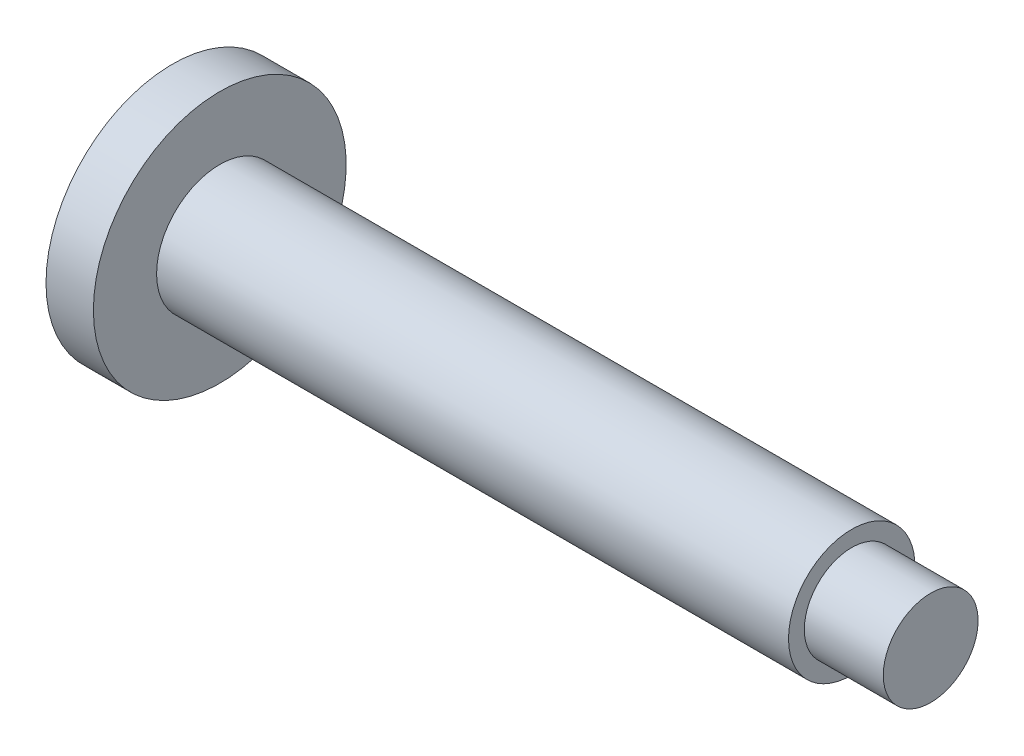
SolidWorks part; units mm, degrees
ref_plane "Front Plane" through (0, 0, 0) normal (0, 0, 1) x (1, 0, 0)
ref_plane "Top Plane" through (0, 0, 0) normal (0, 1, 0) x (1, 0, 0)
ref_plane "Right Plane" through (0, 0, 0) normal (1, 0, 0) x (0, 0, -1)
sketch "Sketch1" plane through (0, 0, 0) normal (0, 0, 1) x (1, 0, 0)
  line L0 (0, 0) -> (52.5167, 0) construction
  line L1 (0, 0) -> (0, 8)
  line L2 (0, 8) -> (3, 8)
  line L3 (3, 8) -> (3, 4)
  line L4 (3, 4) -> (43, 4)
  line L5 (43, 4) -> (43, 3)
  line L6 (43, 3) -> (48, 3)
  line L7 (48, 3) -> (48, 0)
  line L8 (0, 0) -> (48, 0)
  dimension "D1" = 5
  dimension "D2" = 40
  dimension "D3" = 3
  dimension "D4" = 8
  dimension "D5" = 4
revolve "Revolve1" add sketch "Sketch1" angle 360 about L0
cosmetic thread "Cosmetic Thread1" parameters "D1"=5, "D2"=5
